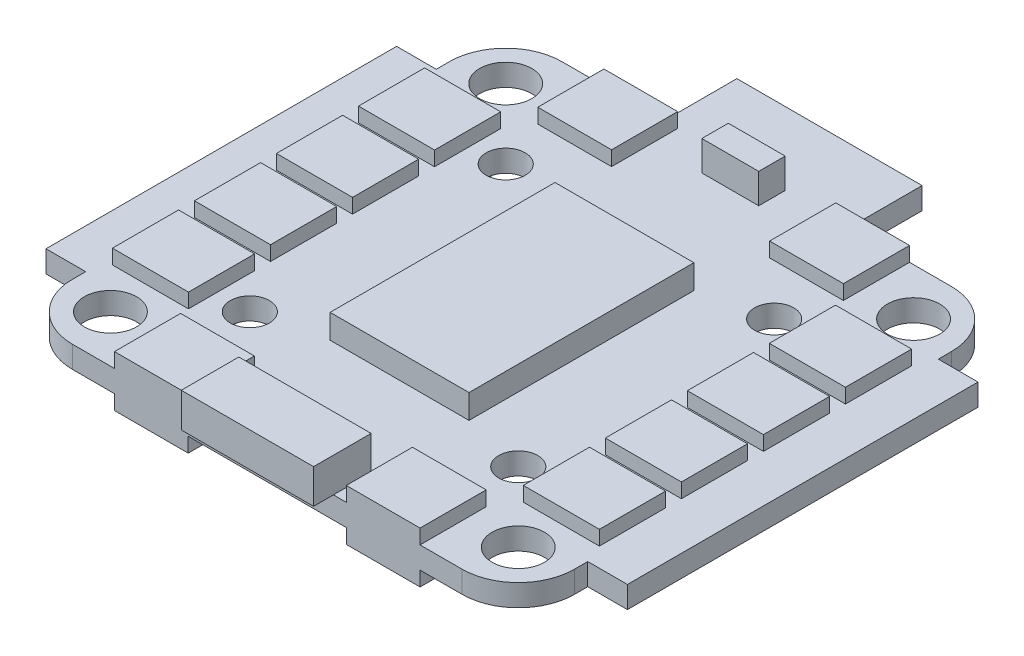
SolidWorks part; units mm, degrees
ref_plane "Front Plane" through (0, 0, 0) normal (0, 0, 1) x (1, 0, 0)
ref_plane "Top Plane" through (0, 0, 0) normal (0, 1, 0) x (1, 0, 0)
ref_plane "Right Plane" through (0, 0, 0) normal (1, 0, 0) x (0, 0, -1)
sketch "Sketch1" plane through (0, 0, 0) normal (0, 1, 0) x (1, 0, 0)
  line L0 (0, 0) -> (0, 86.5739) construction
  line L9 (-7, 42.5) -> (7, 42.5)
  line L10 (7, 42.5) -> (7, 37)
  line L11 (14.725, 37) -> (7, 37)
  line L13 (14.725, 0) -> (-14.725, 0)
  line L16 (-7, 42.5) -> (-7, 37)
  line L17 (18.975, 32.75) -> (18.975, 31.75)
  line L18 (21.975, 31.75) -> (21.975, 5.25)
  line L19 (18.975, 4.25) -> (18.975, 5.25)
  line L20 (15.4144, 33.4394) -> (17.7302, 35.7552) construction
  line L21 (17.7302, 35.7552) -> (16.811, 34.836) construction
  line L22 (21.975, 18.5) -> (10.1335, 18.5) construction
  line L23 (14.725, 37) -> (17.1885, 37) construction
  line L24 (18.975, 5.25) -> (21.975, 5.25)
  line L25 (18.975, 32.75) -> (18.975, 36.1901) construction
  line L26 (21.975, 31.75) -> (18.975, 31.75)
  line L27 (-18.975, 32.75) -> (-18.975, 31.75)
  line L28 (-21.975, 31.75) -> (-21.975, 5.25)
  line L29 (-18.975, 5.25) -> (-21.975, 5.25)
  line L30 (-18.975, 4.25) -> (-18.975, 5.25)
  line L31 (-21.975, 31.75) -> (-18.975, 31.75)
  line L32 (-14.725, 37) -> (-7, 37)
  arc A1 (18.975, 32.75) -> (14.725, 37) centre (14.725, 32.75) ccw
  arc A3 (14.725, 0) -> (18.975, 4.25) centre (14.725, 4.25) ccw
  circle A4 centre (15.4144, 33.4394) radius 1.975
  circle A5 centre (15.4144, 3.5606) radius 1.975
  arc A6 (-14.725, 0) -> (-18.975, 4.25) centre (-14.725, 4.25) cw
  circle A7 centre (-15.4144, 3.5606) radius 1.975
  circle A8 centre (-15.4144, 33.4394) radius 1.975
  arc A9 (-18.975, 32.75) -> (-14.725, 37) centre (-14.725, 32.75) cw
  point P23 (0, 42.5)
  dimension "D3" = 90
  dimension "D4" = 37
  dimension "D7" = 3
  dimension "D9" = 3.95
  dimension "D1" = 5.5
  dimension "D2" = 7
  dimension "D5" = 1.3
  dimension "D6" = 45
  dimension "D8" = 26.5
  dimension "D10" = 21.975
  dimension "D11" = 3
  dimension "D12" = 1
extrude "PCB" add sketch "Sketch1" along normal mid plane 1.65
sketch "Sketch7" plane through (0, 0.825, 0) normal (0, 1, 0) x (1, 0, 0)
  line L0 (21.975, 18.5) -> (-21.975, 18.5) construction
  line L1 (21.975, 5.25) -> (21.975, 31.75) construction
  line L2 (-21.975, 31.75) -> (-21.975, 5.25) construction
  line L3 (0, 42.5) -> (0, -1.4329) construction
  line L4 (7, 42.5) -> (-7, 42.5) construction
  line L5 (15.4144, 33.4394) -> (10.1465, 28.1715) construction
  line L6 (14.725, 37) -> (7, 37) construction
  line L7 (14.0179, 32.0429) -> (11.1895, 29.2145) construction
  circle A0 centre (10.1465, 28.1715) radius 1.475
  circle A1 centre (15.4144, 33.4394) radius 1.975 construction
  circle A2 centre (-10.1465, 28.1715) radius 1.475
  circle A3 centre (-10.1465, 8.8285) radius 1.475
  circle A4 centre (10.1465, 8.8285) radius 1.475
  dimension "D3" = 2.95
  dimension "D1" = 45
  dimension "D2" = 4
extrude "inner holes" cut sketch "Sketch7" against normal through all both and the other way through all
sketch "Sketch8" plane through (0, 0.825, 0) normal (0, 1, 0) x (1, 0, 0)
  line L1 (-5, 2.85) -> (5, 2.85)
  line L2 (-5, 2.85) -> (-5, -1.5)
  line L3 (-5, -1.5) -> (5, -1.5)
  line L4 (5, 2.85) -> (5, -1.5)
  line L5 (-14.725, 0) -> (14.725, 0) construction
  point P4 (0, 2.85)
  dimension "D1" = 10
  dimension "D2" = 4.35
  dimension "D3" = 1.5
extrude "Connector" add sketch "Sketch8" along normal blind 2.6
sketch "Sketch9" plane through (0, 0.825, 0) normal (0, 1, 0) x (1, 0, 0)
  line L0 (-7, 37) -> (-14.725, 37) construction
  line L1 (-2.15, 37) -> (2.15, 37)
  line L2 (-2.15, 37) -> (-2.15, 35)
  line L3 (-2.15, 35) -> (2.15, 35)
  line L4 (2.15, 37) -> (2.15, 35)
  line L5 (0, 42.5) -> (0, 40.4487) construction
  line L6 (7, 42.5) -> (-7, 42.5) construction
  point P12 (0, 37)
  dimension "D1" = 4.3
  dimension "D2" = 2
extrude "Top component" add sketch "Sketch9" along normal blind 2.255
sketch "Sketch10" plane through (0, 0.825, 0) normal (0, 1, 0) x (1, 0, 0)
  line L0 (0, 42.5) -> (0, 11.1465) construction
  line L1 (7, 42.5) -> (-7, 42.5) construction
  line L2 (-21.975, 18.5) -> (21.975, 18.5) construction
  line L3 (-21.975, 31.75) -> (-21.975, 5.25) construction
  line L4 (21.975, 5.25) -> (21.975, 31.75) construction
  line L5 (12.655, 17.9) -> (18.405, 17.9)
  line L6 (12.655, 11.7) -> (18.405, 11.7)
  line L7 (12.655, 11.7) -> (12.655, 6.7)
  line L8 (12.655, 6.7) -> (18.405, 6.7)
  line L9 (18.405, 11.7) -> (18.405, 6.7)
  line L10 (12.655, 17.9) -> (12.655, 12.9)
  line L11 (12.655, 12.9) -> (18.405, 12.9)
  line L12 (18.405, 17.9) -> (18.405, 12.9)
  line L13 (12.655, 24.1) -> (18.405, 24.1)
  line L14 (12.655, 24.1) -> (12.655, 19.1)
  line L15 (12.655, 19.1) -> (18.405, 19.1)
  line L16 (18.405, 24.1) -> (18.405, 19.1)
  line L17 (12.655, 30.3) -> (18.405, 30.3)
  line L18 (12.655, 30.3) -> (12.655, 25.3)
  line L19 (12.655, 25.3) -> (18.405, 25.3)
  line L20 (18.405, 30.3) -> (18.405, 25.3)
  line L21 (5, 0) -> (14.725, 0) construction
  line L24 (-12.655, 6.7) -> (-18.405, 6.7)
  line L25 (-18.405, 11.7) -> (-18.405, 6.7)
  line L26 (-12.655, 11.7) -> (-18.405, 11.7)
  line L27 (-12.655, 11.7) -> (-12.655, 6.7)
  line L28 (-12.655, 17.9) -> (-12.655, 12.9)
  line L29 (-12.655, 12.9) -> (-18.405, 12.9)
  line L30 (-18.405, 17.9) -> (-18.405, 12.9)
  line L31 (-12.655, 17.9) -> (-18.405, 17.9)
  line L32 (-12.655, 24.1) -> (-12.655, 19.1)
  line L33 (-12.655, 19.1) -> (-18.405, 19.1)
  line L34 (-18.405, 24.1) -> (-18.405, 19.1)
  line L35 (-12.655, 24.1) -> (-18.405, 24.1)
  line L36 (-12.655, 30.3) -> (-12.655, 25.3)
  line L37 (-12.655, 25.3) -> (-18.405, 25.3)
  line L38 (-18.405, 30.3) -> (-18.405, 25.3)
  line L39 (-12.655, 30.3) -> (-18.405, 30.3)
  dimension "D1" = 5.75
  dimension "D2" = 5
  dimension "D3" = 1.2
  dimension "D4" = 1.2
  dimension "D5" = 1.2
  dimension "D6" = 3.57
  dimension "D7" = 11.7
extrude "Side Components" add sketch "Sketch10" along normal blind 1.1
sketch "Sketch11" plane through (0, 0.825, 0) normal (0, 1, 0) x (1, 0, 0)
  line L0 (0, 42.5) -> (0, 40.6485) construction
  line L1 (-5.25, 27) -> (5.25, 27)
  line L2 (-5.25, 27) -> (-5.25, 10)
  line L3 (-5.25, 10) -> (5.25, 10)
  line L4 (5.25, 27) -> (5.25, 10)
  line L5 (7, 42.5) -> (-7, 42.5) construction
  line L6 (-21.975, 31.75) -> (-21.975, 5.25) construction
  point P9 (0, 27)
  point P12 (-21.975, 18.5)
  point P13 (-5.25, 18.5)
  dimension "D1" = 10.5
  dimension "D2" = 17
extrude "Central components" add sketch "Sketch11" along normal blind 1.825
sketch "Sketch12" plane through (0, 0.825, 0) normal (0, 1, 0) x (1, 0, 0)
  line L0 (0, 42.5) -> (0, 31.1097) construction
  line L1 (7, 42.5) -> (-7, 42.5) construction
  line L2 (-21.975, 18.5) -> (21.975, 18.5) construction
  line L3 (-21.975, 31.75) -> (-21.975, 5.25) construction
  line L4 (21.975, 5.25) -> (21.975, 31.75) construction
  line L5 (14.725, 37) -> (7, 37) construction
  line L6 (5.975, 37) -> (11.55, 37)
  line L7 (5.975, 37) -> (5.975, 32)
  line L8 (5.975, 32) -> (11.55, 32)
  line L9 (11.55, 37) -> (11.55, 32)
  line L10 (5.975, 5) -> (11.55, 5)
  line L11 (11.55, 0) -> (11.55, 5)
  line L12 (5.975, 0) -> (11.55, 0)
  line L13 (5.975, 0) -> (5.975, 5)
  line L14 (-5.975, 0) -> (-5.975, 5)
  line L15 (-5.975, 0) -> (-11.55, 0)
  line L16 (-11.55, 0) -> (-11.55, 5)
  line L17 (-5.975, 5) -> (-11.55, 5)
  line L18 (-5.975, 32) -> (-11.55, 32)
  line L19 (-11.55, 37) -> (-11.55, 32)
  line L20 (-5.975, 37) -> (-11.55, 37)
  line L21 (-5.975, 37) -> (-5.975, 32)
  dimension "D1" = 5.575
  dimension "D2" = 16
  dimension "D3" = 5
extrude "Top and bottom components" add sketch "Sketch12" along normal blind 1.105
mirror "Mirror2" about plane through (0, 0, 0) normal (0, 1, 0) of "Side Components", "Top and bottom components"
